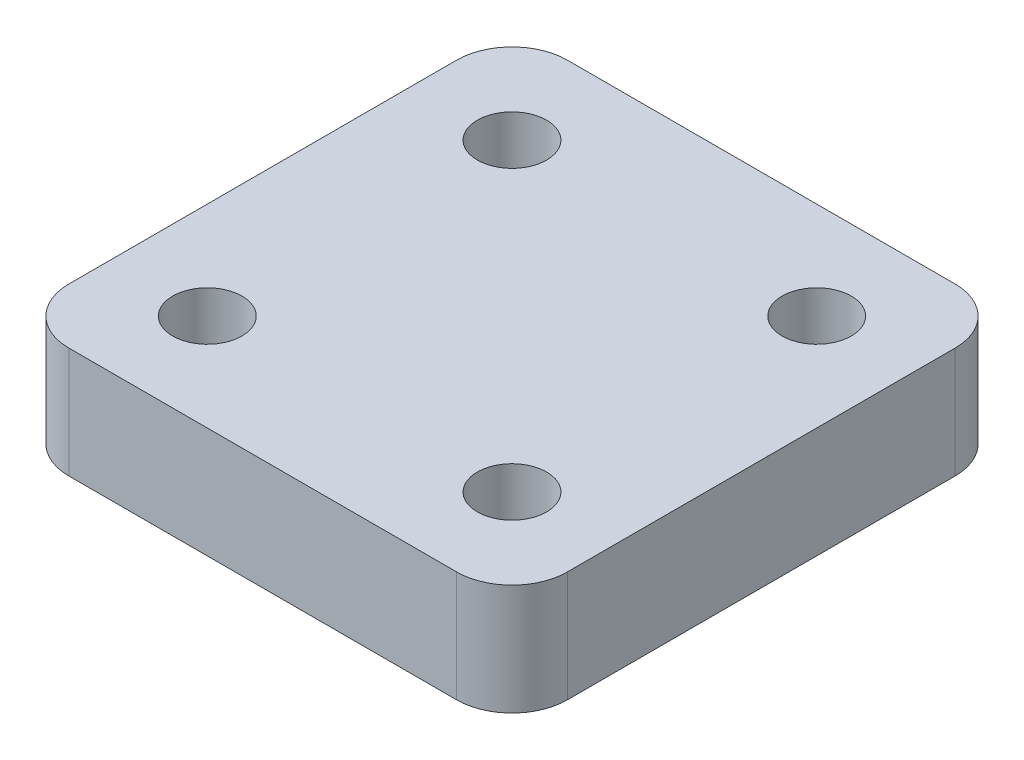
SolidWorks part; units mm, degrees
ref_plane "Front Plane" through (0, 0, 0) normal (0, 0, 1) x (1, 0, 0)
ref_plane "Top Plane" through (0, 0, 0) normal (0, 1, 0) x (1, 0, 0)
ref_plane "Right Plane" through (0, 0, 0) normal (1, 0, 0) x (0, 0, -1)
sketch "Çizim1" plane through (0, 0, 0) normal (0, 1, 0) x (1, 0, 0)
  line L0 (-900, 700) -> (-900, -700)
  line L1 (-700, -900) -> (700, -900)
  line L2 (900, -700) -> (900, 700)
  line L3 (-700, 900) -> (700, 900)
  circle A0 centre (-550, 550) radius 125
  circle A1 centre (550, 550) radius 125
  circle A2 centre (-550, -550) radius 125
  circle A3 centre (550, -550) radius 125
  arc A4 (900, 700) -> (700, 900) centre (700, 700) ccw
  arc A5 (900, -700) -> (700, -900) centre (700, -700) cw
  arc A6 (-900, -700) -> (-700, -900) centre (-700, -700) ccw
  arc A7 (-900, 700) -> (-700, 900) centre (-700, 700) cw
  point P16 (900, 900)
  point P19 (900, -900)
  point P22 (-900, -900)
  point P25 (-900, 900)
  dimension "D1" = 550
  dimension "D3" = 250
  dimension "D4" = 250
  dimension "D5" = 1100
  dimension "D15" = 200
  dimension "D2" = 550
  dimension "D6" = 1100
  dimension "D7" = 1100
  dimension "D8" = 550
  dimension "D9" = 550
  dimension "D10" = 900
  dimension "D11" = 900
  dimension "D12" = 900
  dimension "D13" = 900
  dimension "D14" = 900
extrude "Yükseklik-Ekstrüzyon2" add sketch "Çizim1" along normal blind 400
sketch "Çizim2" plane through (0, 0, 0) normal (0, -1, 0) x (1, 0, 0)
  circle A0 centre (0, 0) radius 530
extrude "Kes-Ekstrüzyon1" cut sketch "Çizim2" against normal blind 150
sketch "Çizim3" plane through (0, 150, 0) normal (0, -1, 0) x (1, 0, 0)
  circle A0 centre (0, 0) radius 540
  dimension "D1" = 1080
extrude "Yükseklik-Ekstrüzyon3" add sketch "Çizim3" along normal blind 300
